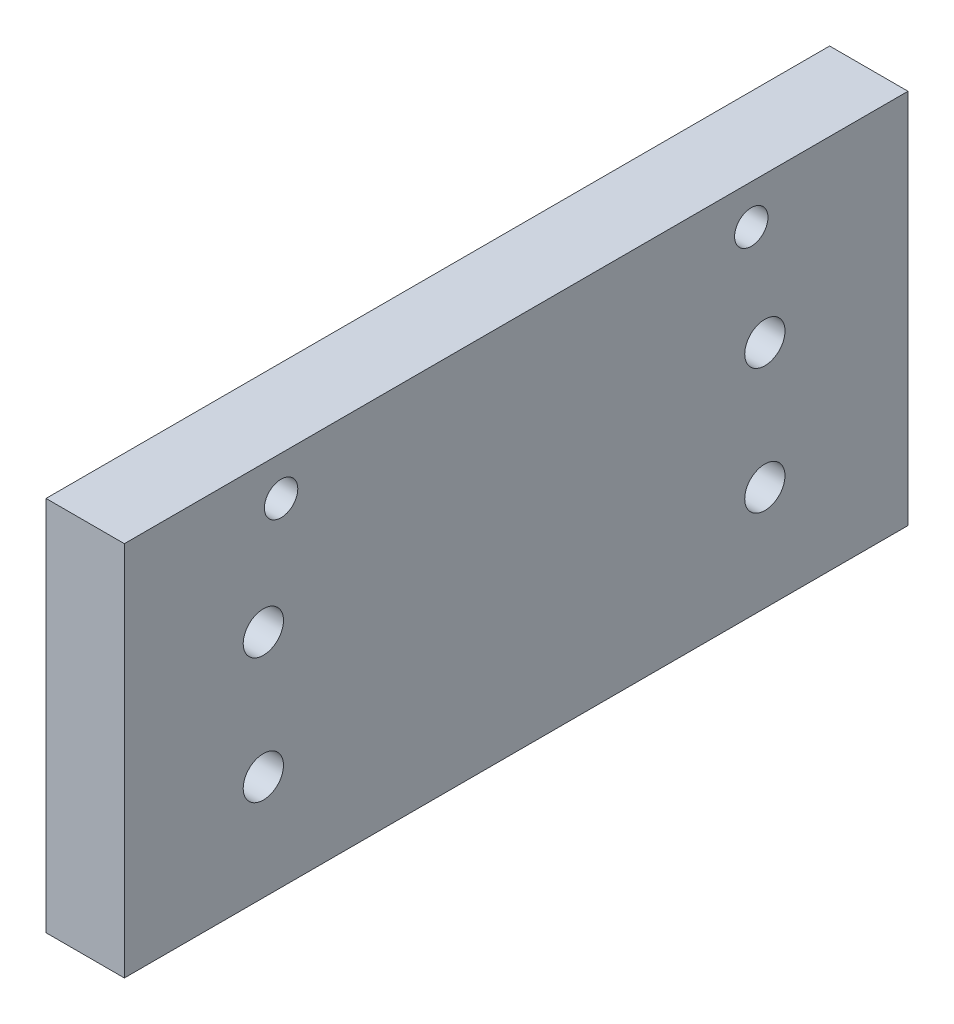
SolidWorks part; units mm, degrees
ref_plane "Front Plane" through (0, 0, 0) normal (0, 0, 1) x (1, 0, 0)
ref_plane "Top Plane" through (0, 0, 0) normal (0, 1, 0) x (1, 0, 0)
ref_plane "Right Plane" through (0, 0, 0) normal (1, 0, 0) x (0, 0, -1)
sketch "Sketch1" plane through (0, 0, 0) normal (1, 0, 0) x (0, 0, -1)
  line L1 (-60.2649, 35.4411) -> (3.2351, 35.4411)
  line L2 (-60.2649, 35.4411) -> (-60.2649, 4.9611)
  line L3 (-60.2649, 4.9611) -> (3.2351, 4.9611)
  line L4 (3.2351, 35.4411) -> (3.2351, 4.9611)
  dimension "D1" = 63.5
  dimension "D2" = 30.48
extrude "Boss-Extrude1" add sketch "Sketch1" along normal blind 6.35
hole_wizard "#8 (0.199) Diameter Hole1" positions "Sketch3" profile "Sketch2" hole size "#8" standard "Ansi Inch"
sketch "Sketch3" plane through (0, 0, 0) normal (-1, 0, 0) x (0, 0, 1)
  line L0 (60.2649, 35.4411) -> (60.2649, 4.9611) construction
  line L1 (60.2649, 4.9611) -> (-3.2351, 4.9611) construction
  point P0 (12.6399, 11.3111)
  point P1 (44.3899, 11.3111)
  dimension "D1" = 31.75
  dimension "D2" = 15.875
  dimension "D3" = 6.35
  dimension "D4" = 6.35
sketch "Sketch2" plane through (0, 11.3111, 12.6399) normal (0, 1, 0) x (0, 0, 1)
  line L0 (0, 0) -> (0, 7.8686)
  line L1 (0, 7.8686) -> (2.5273, 6.35)
  line L2 (2.5273, 6.35) -> (2.5273, 0)
  line L5 (2.5273, 0) -> (0, 0)
  line L10 (0, 7.8686) -> (-2.5273, 6.35) construction
  line L11 (0, -6.35) -> (0, 107.95) construction
  dimension "Hole Dia." = 5.0546
  dimension "Hole Depth" = 6.35
  dimension "Drill Angle" = 118
hole_wizard "Tap Drill for #6-32 Tap1" positions "Sketch7" profile "Sketch6" hole size "#6-32" standard "Ansi Inch" end condition up to next
sketch "Sketch7" plane through (0, 0, 0) normal (-1, 0, 0) x (0, 0, 1)
  line L0 (-3.2351, 35.4411) -> (60.2649, 35.4411) construction
  line L1 (-3.2351, 4.9611) -> (-3.2351, 35.4411) construction
  point P0 (9.4649, 32.2661)
  point P1 (47.5649, 32.2661)
  dimension "D1" = 3.175
  dimension "D2" = 3.175
  dimension "D3" = 38.1
  dimension "D4" = 12.7
sketch "Sketch6" plane through (0, 32.2661, 9.4649) normal (0, 1, 0) x (0, 0, 1)
  line L0 (0, 0) -> (0, 6.35)
  line L1 (0, 6.35) -> (1.3525, 6.35)
  line L2 (1.3525, 6.35) -> (1.3525, 0.635)
  line L3 (1.3525, 0.635) -> (1.9875, 0)
  line L5 (1.9875, 0) -> (0, 0)
  line L6 (-1.3525, 0.635) -> (-1.9875, 0) construction
  line L11 (0, -6.35) -> (0, 107.95) construction
  dimension "Thru Hole Dia." = 2.7051
  dimension "Thru Hole Depth" = 6.35
  dimension "Near C'Sink Dia." = 3.9751
  dimension "Near C'Sink Angle" = 90
hole_wizard "#5 Clearance Hole1" positions "Sketch9" profile "Sketch8" hole size "#5" standard "Ansi Inch"
sketch "Sketch9" plane through (0, 0, 0) normal (-1, 0, 0) x (0, 0, 1)
  point P0 (8.3635, 23.6087)
sketch "Sketch8" plane through (0, 23.6087, 8.3635) normal (0, 1, 0) x (0, 0, 1)
  line L0 (0, 0) -> (0, 13.6806)
  line L1 (0, 13.6806) -> (1.6319, 12.7)
  line L2 (1.6319, 12.7) -> (1.6319, 0)
  line L5 (1.6319, 0) -> (0, 0)
  line L10 (0, 13.6806) -> (-1.6319, 12.7) construction
  line L11 (0, -6.35) -> (0, 107.95) construction
  dimension "Hole Dia." = 3.2639
  dimension "Hole Depth" = 12.7
  dimension "Drill Angle" = 118
pattern_linear "LPattern1" count 2 spacing 40.64 along (0, 0, 1) count 2 spacing 10.16 along (0, -1, 0) of "#5 Clearance Hole1"
equation "\"D2@Sketch3\" = (\"D1@Sketch1\"-\"D1@Sketch3\")/2"
equation "\"D4@Sketch7\" =( \"D1@Sketch1\"-\"D3@Sketch7\")/2"
equation "\"D1@Sketch7\" = \"D2@Sketch7\""
equation "\"D4@Sketch3\" = \"D3@Sketch3\""
